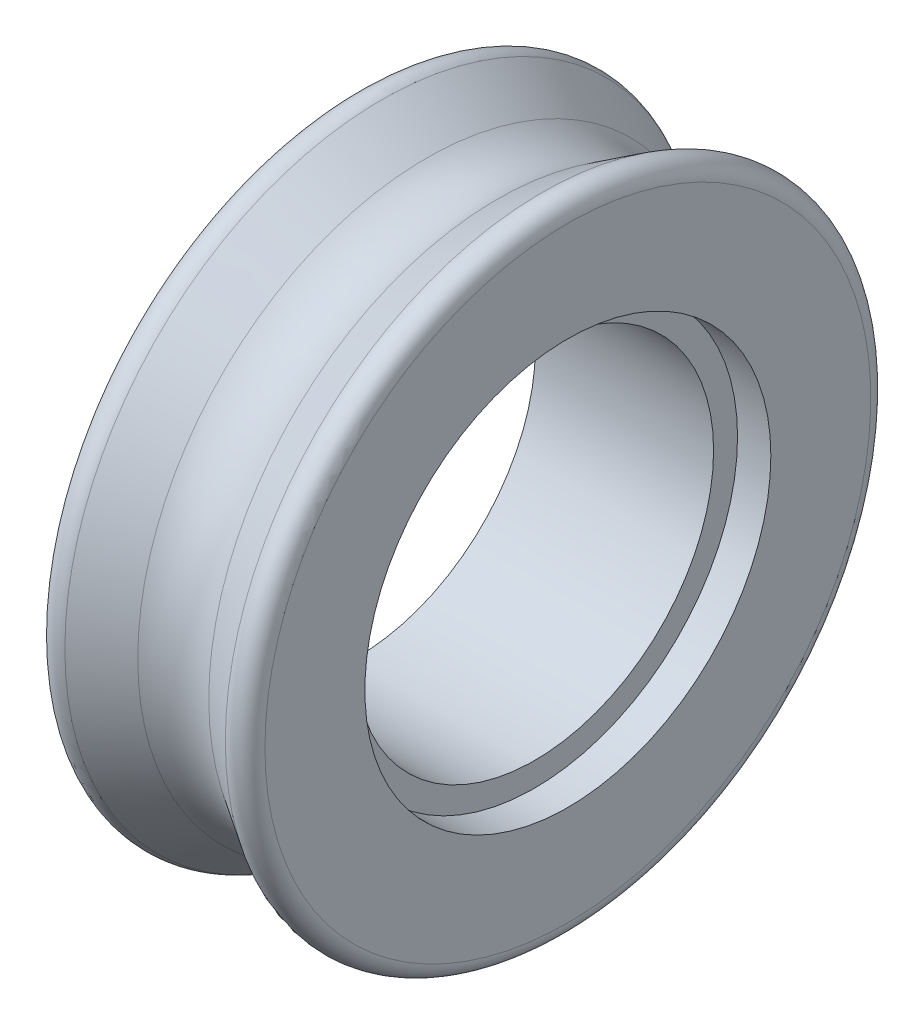
SolidWorks part; units mm, degrees
ref_plane "Front Plane" through (0, 0, 0) normal (0, 0, 1) x (1, 0, 0)
ref_plane "Top Plane" through (0, 0, 0) normal (0, 1, 0) x (1, 0, 0)
ref_plane "Right Plane" through (0, 0, 0) normal (1, 0, 0) x (0, 0, -1)
sketch "Sketch1" plane through (0, 0, 0) normal (0, 0, 1) x (1, 0, 0)
  line L0 (0, 0) -> (0, 10)
  line L1 (0, 10) -> (6.35, 10)
  line L2 (3.175, 10) -> (3.175, 13.2611) construction
  line L3 (0, 10) -> (3.175, 8)
  line L4 (6.35, 10) -> (3.175, 8)
  line L5 (0, 0) -> (6.35, 0)
  line L6 (6.35, 0) -> (6.35, 10)
  dimension "D1" = 10
  dimension "D2" = 6.35
  dimension "D3" = 2
revolve "Revolve1" add sketch "Sketch1" angle 360 about L5
fillet "Fillet1" radius 0.5 2 edges at (6.35, 0, 10) (0, 0, 10)
fillet "Fillet2" radius 2 1 edges at (3.175, 0, 8)
sketch "Sketch2" plane through (6.35, 0, 0) normal (1, 0, 0) x (0, 0, -1)
  circle A2 centre (0, 0) radius 6.0941
  circle A3 centre (0, 0) radius 6.0941
  dimension "D1" = 3
extrude "Cut-Extrude1" cut sketch "Sketch2" against normal blind 1
sketch "Sketch3" plane through (5.35, 0, 0) normal (1, 0, 0) x (0, 0, -1)
  circle A0 centre (0, 0) radius 5.375
  dimension "D1" = 10.75
extrude "Cut-Extrude2" cut sketch "Sketch3" against normal through all
